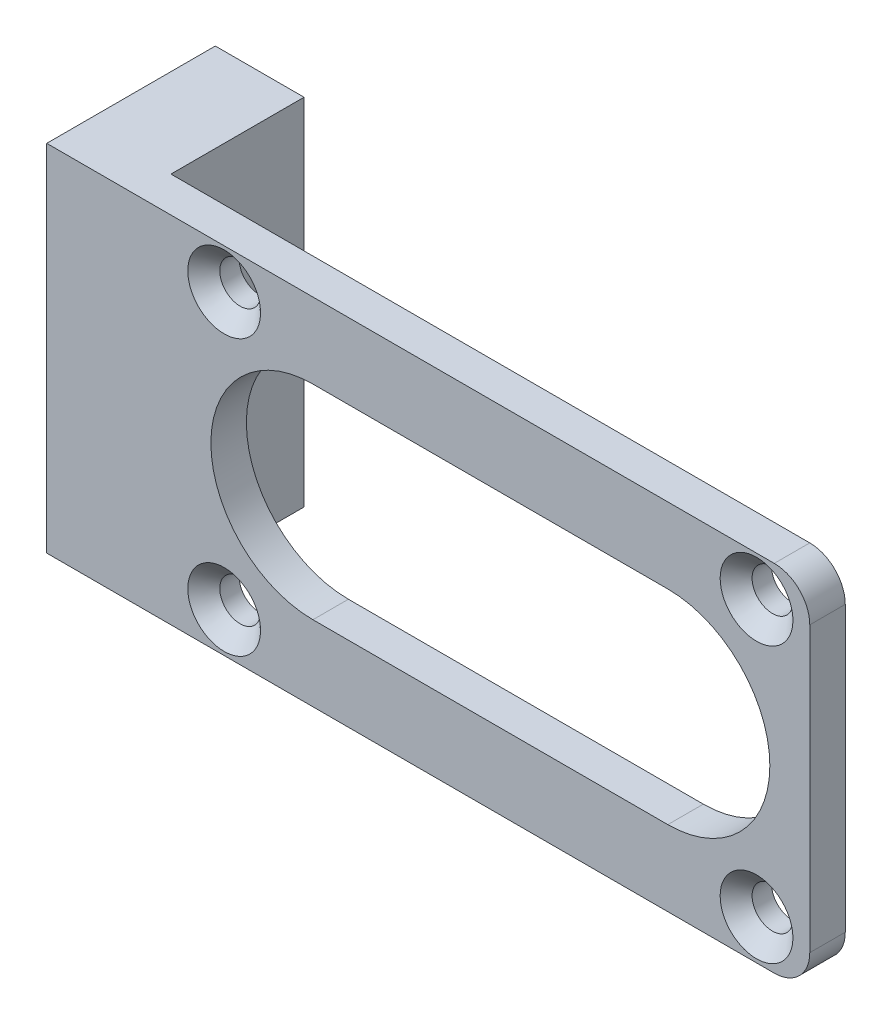
SolidWorks part; units mm, degrees
ref_plane "Front Plane" through (0, 0, 0) normal (0, 0, 1) x (1, 0, 0)
ref_plane "Top Plane" through (0, 0, 0) normal (0, 1, 0) x (1, 0, 0)
ref_plane "Right Plane" through (0, 0, 0) normal (1, 0, 0) x (0, 0, -1)
sketch "Sketch1" plane through (0, 0, 0) normal (0, 0, 1) x (1, 0, 0)
  line L1 (0, 0) -> (38, 0)
  line L2 (0, 0) -> (0, 20)
  line L3 (0, 20) -> (38, 20)
  line L4 (38, 0) -> (38, 20)
  dimension "D1" = 38
  dimension "D2" = 20
extrude "Boss-Extrude1" add sketch "Sketch1" along normal blind 2
sketch "Sketch2" plane through (0, 0, 2) normal (0, 0, 1) x (1, 0, 0)
  line L0 (0, 0) -> (38, 0) construction
  line L1 (0, 20) -> (-5, 20)
  line L2 (0, 20) -> (0, 0)
  line L3 (0, 0) -> (-5, 0)
  line L4 (-5, 20) -> (-5, 0)
  dimension "D1" = 5
extrude "Boss-Extrude2" add sketch "Sketch2" against normal blind 7
sketch "Sketch3" plane through (-5, 0, 0) normal (-1, 0, 0) x (0, 0, 1)
  line L0 (0, 20) -> (0, 0) construction
  line L1 (0, 20) -> (0, 0) construction
  line L2 (-5, 20) -> (2, 20) construction
  line L4 (-5, 20) -> (-5, 0) construction
  circle A0 centre (-2.5, 10) radius 1.5
  dimension "D1" = 3
  dimension "D2" = 20
  dimension "D3" = 10
  dimension "D4" = 5
  dimension "D5" = 2.5
hole_wizard "M3 Tapped Hole1" positions "3DSketch4" profile "Sketch6" tap size "M3" standard "ISO" end condition through all
sketch3d "3DSketch4"
  point P0 (-5, 10, -2.5)
sketch "Sketch6" plane through (-5, 10, -2.5) normal (0, 1, 0) x (0, 0, 1)
  line L0 (0, 0) -> (0, 43)
  line L1 (0, 43) -> (1.25, 43)
  line L2 (1.25, 43) -> (1.25, 0)
  line L5 (1.25, 0) -> (0, 0)
  line L11 (0, -6.35) -> (0, 107.95) construction
  dimension "Thru Tap Drill Dia." = 2.5
  dimension "Thru Tap Drill Depth" = 43
cosmetic thread "Hole Thread1" parameters "D2"=3
sketch "Sketch7" plane through (0, 0, 2) normal (0, 0, 1) x (1, 0, 0)
  line L0 (38, 10) -> (-5, 10) construction
  line L1 (38, 0) -> (38, 20) construction
  line L2 (-5, 20) -> (-5, 0) construction
  circle A1 centre (35, 17.75) radius 1.15
  circle A2 centre (5, 17.75) radius 1.15
  circle A4 centre (35, 2.25) radius 1.15
  circle A5 centre (5, 2.25) radius 1.15
  dimension "D1" = 15.5
  dimension "D2" = 30
  dimension "D3" = 2.3
  dimension "D5" = 5
extrude "Cut-Extrude1" cut sketch "Sketch7" against normal blind 7.5
sketch "Sketch8" plane through (0, 0, 2) normal (0, 0, 1) x (1, 0, 0)
  line L0 (38, 10) -> (-5, 10) construction
  line L1 (38, 0) -> (38, 20) construction
  line L2 (-5, 20) -> (-5, 0) construction
  line L3 (30, 10) -> (10, 10) construction
  line L4 (30, 4.25) -> (10, 4.25)
  line L5 (30, 15.75) -> (10, 15.75)
  arc A0 (30, 4.25) -> (30, 15.75) centre (30, 10) ccw
  arc A1 (10, 15.75) -> (10, 4.25) centre (10, 10) ccw
  point P8 (20, 10)
  dimension "D2" = 8
  dimension "D3" = 11.5
  dimension "D1" = 20
extrude "Cut-Extrude2" cut sketch "Sketch8" against normal blind 7.5
sketch "Sketch9" plane through (0, 0, -5) normal (0, 0, -1) x (-1, 0, 0)
  line L4 (0, 20) -> (0, 0)
  line L5 (0, 0) -> (5, 0)
  line L6 (5, 0) -> (5, 20)
  line L7 (5, 20) -> (0, 20)
  line L8 (0, 20) -> (0, 0)
  line L9 (0, 0) -> (5, 0)
  line L10 (5, 0) -> (5, 20)
  line L11 (5, 20) -> (0, 20)
  dimension "D1" = 0
extrude "Boss-Extrude3" add sketch "Sketch9" along normal blind 2.5
fillet "Fillet1" radius 2 2 edges at (38, 0, 1) (38, 20, 1)
chamfer "Chamfer1" distance 0.9 angle 45 4 edges at (3.85, 2.25, 2) (33.85, 2.25, 2) (36.15, 17.75, 2) (6.15, 17.75, 2)
sketch "Sketch10" plane through (0, 0, 2) normal (0, 0, 1) x (1, 0, 0)
  circle A0 centre (5, 17.75) radius 2.05 construction
  circle A1 centre (5, 17.75) radius 2.05
  dimension "D1" = 4.1
equation "\"D3@Sketch3\"=\"D2@Sketch3\"/2"
equation "\"D5@Sketch3\"=\"D4@Sketch3\"/2"
